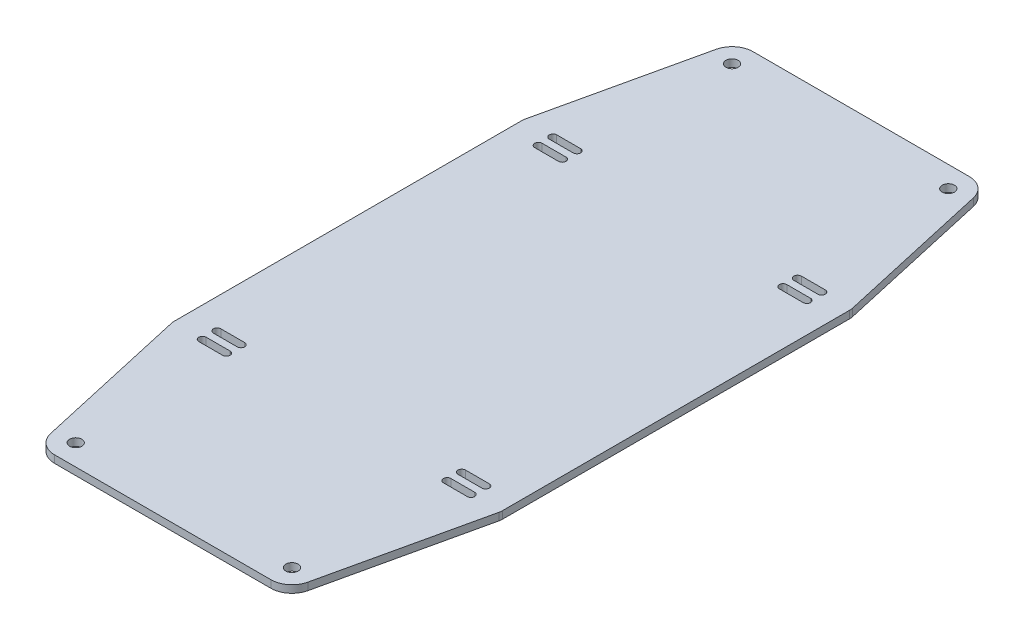
SolidWorks part; units mm, degrees
ref_plane "Front Plane" through (0, 0, 0) normal (0, 0, 1) x (1, 0, 0)
ref_plane "Top Plane" through (0, 0, 0) normal (0, 1, 0) x (1, 0, 0)
ref_plane "Right Plane" through (0, 0, 0) normal (1, 0, 0) x (0, 0, -1)
sketch "Sketch1" plane through (0, 0, 0) normal (0, 1, 0) x (1, 0, 0)
  line L1 (-139.979, 87.3459) -> (143.4878, 87.3459)
  line L2 (-139.979, 87.3459) -> (-139.979, -95.8674)
  line L3 (-139.979, -95.8674) -> (143.4878, -95.8674)
  line L4 (143.4878, 87.3459) -> (143.4878, -95.8674)
  dimension "D1" = 283.4668
  dimension "D2" = 183.2133
extrude "Boss-Extrude1" add sketch "Sketch1" along normal blind 3.175
sketch "Sketch2" plane through (0, 3.175, 0) normal (0, 1, 0) x (1, 0, 0)
  line L0 (14.6126, 63.1663) -> (128.9126, 63.1663)
  line L1 (14.6126, -79.8357) -> (128.9126, -79.8357)
  line L2 (14.6126, -79.8357) -> (14.6126, 66.2143)
  line L3 (14.6126, 66.2143) -> (128.9126, 66.2143)
  line L4 (128.9126, -79.8357) -> (128.9126, 66.2143)
  line L5 (14.6126, 61.5788) -> (24.7726, 61.5788) construction
  line L6 (14.6126, 63.1663) -> (24.7726, 63.1663)
  line L7 (14.6126, 59.9913) -> (24.7726, 59.9913)
  line L8 (14.6126, 67.8018) -> (24.7726, 67.8018) construction
  line L9 (14.6126, 69.3893) -> (24.7726, 69.3893)
  line L10 (14.6126, 66.2143) -> (24.7726, 66.2143)
  line L11 (118.7526, 61.5788) -> (128.9126, 61.5788) construction
  line L12 (118.7526, 63.1663) -> (128.9126, 63.1663)
  line L13 (118.7526, 59.9913) -> (128.9126, 59.9913)
  line L14 (118.7526, 67.8018) -> (128.9126, 67.8018) construction
  line L15 (118.7526, 69.3893) -> (128.9126, 69.3893)
  line L16 (118.7526, 66.2143) -> (128.9126, 66.2143)
  line L17 (14.6126, -6.8107) -> (128.9126, -6.8107)
  line L18 (118.7526, -75.2002) -> (128.9126, -75.2002) construction
  line L19 (118.7526, -76.7877) -> (128.9126, -76.7877)
  line L20 (118.7526, -73.6127) -> (128.9126, -73.6127)
  line L21 (118.7526, -81.4232) -> (128.9126, -81.4232) construction
  line L22 (118.7526, -83.0107) -> (128.9126, -83.0107)
  line L23 (118.7526, -79.8357) -> (128.9126, -79.8357)
  line L24 (14.6126, -75.2002) -> (24.7726, -75.2002) construction
  line L25 (14.6126, -76.7877) -> (24.7726, -76.7877)
  line L26 (14.6126, -73.6127) -> (24.7726, -73.6127)
  line L27 (14.6126, -81.4232) -> (24.7726, -81.4232) construction
  line L28 (14.6126, -83.0107) -> (24.7726, -83.0107)
  line L29 (14.6126, -79.8357) -> (24.7726, -79.8357)
  line L31 (1.9126, -79.8357) -> (1.9126, 78.9143)
  line L32 (1.9126, 78.9143) -> (141.6126, 78.9143)
  line L33 (141.6126, -79.8357) -> (141.6126, 78.9143)
  line L34 (14.6126, -67.1357) -> (128.9126, -67.1357)
  line L35 (14.6126, -92.5357) -> (128.9126, -92.5357)
  line L36 (128.9126, -92.5357) -> (141.6126, -92.5357)
  line L37 (141.6126, -92.5357) -> (141.6126, -79.8357)
  line L38 (14.6126, -92.5357) -> (1.9126, -92.5357)
  line L39 (1.9126, -92.5357) -> (1.9126, -79.8357)
  arc A0 (14.6126, 63.1663) -> (14.6126, 59.9913) centre (14.6126, 61.5788) ccw
  arc A1 (24.7726, 59.9913) -> (24.7726, 63.1663) centre (24.7726, 61.5788) ccw
  arc A2 (14.6126, 69.3893) -> (14.6126, 66.2143) centre (14.6126, 67.8018) ccw
  arc A3 (24.7726, 66.2143) -> (24.7726, 69.3893) centre (24.7726, 67.8018) ccw
  arc A4 (118.7526, 63.1663) -> (118.7526, 59.9913) centre (118.7526, 61.5788) ccw
  arc A5 (128.9126, 59.9913) -> (128.9126, 63.1663) centre (128.9126, 61.5788) ccw
  arc A6 (118.7526, 69.3893) -> (118.7526, 66.2143) centre (118.7526, 67.8018) ccw
  arc A7 (128.9126, 66.2143) -> (128.9126, 69.3893) centre (128.9126, 67.8018) ccw
  arc A8 (118.7526, -76.7877) -> (118.7526, -73.6127) centre (118.7526, -75.2002) cw
  arc A9 (128.9126, -73.6127) -> (128.9126, -76.7877) centre (128.9126, -75.2002) cw
  arc A10 (118.7526, -83.0107) -> (118.7526, -79.8357) centre (118.7526, -81.4232) cw
  arc A11 (128.9126, -79.8357) -> (128.9126, -83.0107) centre (128.9126, -81.4232) cw
  arc A12 (14.6126, -76.7877) -> (14.6126, -73.6127) centre (14.6126, -75.2002) cw
  arc A13 (24.7726, -73.6127) -> (24.7726, -76.7877) centre (24.7726, -75.2002) cw
  arc A14 (14.6126, -83.0107) -> (14.6126, -79.8357) centre (14.6126, -81.4232) cw
  arc A15 (24.7726, -79.8357) -> (24.7726, -83.0107) centre (24.7726, -81.4232) cw
  point P8 (19.6926, 61.5788)
  point P17 (19.6926, 67.8018)
  point P22 (123.8326, -75.2002)
  point P26 (123.8326, 61.5788)
  point P33 (123.8326, 67.8018)
  point P45 (123.8326, -81.4232)
  point P51 (19.6926, -75.2002)
  point P58 (19.6926, -81.4232)
  line M5 (-139.979, 87.3459) -> (-139.979, -95.8674)
  line M6 (-139.979, -95.8674) -> (143.4878, -95.8674)
  line M7 (143.4878, -95.8674) -> (143.4878, 87.3459)
  line M8 (143.4878, 87.3459) -> (-139.979, 87.3459)
  dimension "D1" = 12.7
  dimension "D2" = 114.3
  dimension "D3" = 12.7
extrude "Cut-Extrude1" cut sketch "Sketch2" against normal through all contours L38 L39 L31 L32 L33 L37 L36 L35 M8 M5 M6 M7 | L7 A1 L0 L2 | L2 A0 | L3 A3 L9 A2 | L0 A4 L13 L4 | L3 A7 L15 A6 | A11 L1 A10 L22 | A9 L4 | A8 L19 L4 L20 | L4 A5 | A15 L1 A14 L28 | A13 L26 L2 L25 | A12 L2
sketch "Sketch4" plane through (0, 3.175, 0) normal (0, 1, 0) x (1, 0, 0)
  line L1 (141.6126, 78.9143) -> (141.6126, 220.5913)
  line L2 (141.6126, -92.5357) -> (141.6126, -210.8334)
  line L3 (1.9126, 78.9143) -> (141.6126, 78.9143)
  line L4 (1.9126, 78.9143) -> (1.9126, 155.1143)
  line L5 (1.9126, 155.1143) -> (141.6126, 155.1143)
  line L6 (141.6126, 78.9143) -> (141.6126, 155.1143)
  line L8 (1.9126, -92.5357) -> (141.6126, -92.5357)
  line L9 (1.9126, -92.5357) -> (1.9126, -168.7357)
  line L10 (1.9126, -168.7357) -> (141.6126, -168.7357)
  line L11 (141.6126, -92.5357) -> (141.6126, -168.7357)
  line M19 (1.9126, -92.5357) -> (141.6126, -92.5357)
  line M21 (141.6126, 78.9143) -> (1.9126, 78.9143)
  dimension "D1" = 76.2
  dimension "D2" = 76.2
extrude "Boss-Extrude2" add sketch "Sketch4" against normal blind 3.175 contours L5 L4 L1 M21 | L9 L10 L2 M19
sketch "Sketch3" plane through (0, 3.175, 0) normal (0, 1, 0) x (1, 0, 0)
  line L0 (141.6126, -92.5357) -> (1.9126, -92.5357) construction
  line L5 (1.9126, 78.9143) -> (141.6126, 78.9143)
  line L6 (1.9126, 78.9143) -> (1.9126, -92.5357)
  line L7 (1.9126, -92.5357) -> (141.6126, -92.5357)
  line L8 (141.6126, 78.9143) -> (141.6126, -92.5357)
  line L9 (1.9126, 78.9143) -> (141.6126, -92.5357) construction
  line L10 (1.9126, -92.5357) -> (141.6126, 78.9143) construction
  line L11 (1.9126, 78.9143) -> (141.6126, 78.9143) construction
  line L12 (141.6126, -168.7357) -> (141.6126, 155.1143) construction
  line L13 (1.9126, -168.7357) -> (1.9126, 155.1143) construction
  line L15 (117.8001, 132.8893) -> (25.7251, 132.8893)
  line L16 (117.8001, 132.8893) -> (117.8001, -146.5107)
  line L17 (117.8001, -146.5107) -> (25.7251, -146.5107)
  line L18 (25.7251, 132.8893) -> (25.7251, -146.5107)
  line L19 (117.8001, 132.8893) -> (25.7251, -146.5107) construction
  line L20 (117.8001, -146.5107) -> (25.7251, 132.8893) construction
  circle A0 centre (117.8001, 132.8893) radius 2.6
  circle A1 centre (117.8001, -146.5107) radius 2.6
  circle A2 centre (25.7251, -146.5107) radius 2.6
  circle A3 centre (25.7251, 132.8893) radius 2.6
  point P0 (71.7626, -6.8107)
  point P4 (71.7626, -6.8107)
  dimension "D3" = 5.2
  dimension "D4" = 5.2
  dimension "D5" = 5.2
  dimension "D6" = 5.2
  dimension "D1" = 279.4
  dimension "D2" = 92.075
extrude "Cut-Extrude2" cut sketch "Sketch3" against normal through all contours L15 A3 L18 | L18 A3 L15 | L16 A0 L15 | L15 A0 L16 | L17 A1 L16 | L16 A1 L17 | L18 A2 L17 | L17 A2 L18
sketch "Sketch5" plane through (0, 3.175, 0) normal (0, 1, 0) x (1, 0, 0)
  line L8 (16.9933, 134.8532) -> (1.9126, 67.8018)
  line L9 (126.532, 134.8532) -> (141.6126, 67.8018)
  line L10 (141.6126, -81.4232) -> (126.532, -148.4746)
  line L11 (16.9933, -148.4746) -> (1.9126, -81.4232)
  line L12 (117.8001, 141.8393) -> (25.7251, 141.8393)
  line L13 (117.8001, -155.4607) -> (25.7251, -155.4607)
  line L14 (141.6126, -168.7357) -> (141.6126, 155.1143) construction
  line L15 (141.6126, 67.8018) -> (141.6126, -81.4232)
  line L16 (1.9126, -168.7357) -> (1.9126, 155.1143) construction
  line L17 (1.9126, 67.8018) -> (1.9126, -81.4232)
  circle A2 centre (117.8001, 132.8893) radius 8.95
  circle A3 centre (117.8001, 132.8893) radius 8.95
  circle A5 centre (25.7251, 132.8893) radius 8.95
  circle A6 centre (25.7251, 132.8893) radius 8.95
  circle A8 centre (25.7251, -146.5107) radius 8.95
  circle A9 centre (25.7251, -146.5107) radius 8.95
  circle A11 centre (117.8001, -146.5107) radius 8.95
  circle A12 centre (117.8001, -146.5107) radius 8.95
  arc A14 (128.9126, -89.3607) -> (128.9126, -73.4857) centre (128.9126, -81.4232) ccw
  arc A15 (128.9126, -89.3607) -> (128.9126, -73.4857) centre (128.9126, -81.4232) ccw
  arc A17 (128.9126, 59.8643) -> (128.9126, 75.7393) centre (128.9126, 67.8018) ccw
  arc A18 (128.9126, 59.8643) -> (128.9126, 75.7393) centre (128.9126, 67.8018) ccw
  arc A20 (14.6126, -73.4857) -> (14.6126, -89.3607) centre (14.6126, -81.4232) ccw
  arc A21 (14.6126, -73.4857) -> (14.6126, -89.3607) centre (14.6126, -81.4232) ccw
  arc A23 (14.6126, 75.7393) -> (14.6126, 59.8643) centre (14.6126, 67.8018) ccw
  arc A24 (14.6126, 75.7393) -> (14.6126, 59.8643) centre (14.6126, 67.8018) ccw
  line M29 (1.9126, 155.1143) -> (1.9126, -168.7357)
  line M30 (1.9126, -168.7357) -> (141.6126, -168.7357)
  line M31 (141.6126, -168.7357) -> (141.6126, 155.1143)
  line M32 (141.6126, 155.1143) -> (1.9126, 155.1143)
  dimension "D1" = 6.35
  dimension "D2" = 6.35
  dimension "D3" = 6.35
  dimension "D4" = 6.35
  dimension "D5" = 6.35
  dimension "D6" = 6.35
  dimension "D7" = 6.35
  dimension "D8" = 6.35
extrude "Cut-Extrude3" cut sketch "Sketch5" against normal through all both and the other way through all contours A6 L12 A3 L9 L8 M31 M32 M29 | A12 L13 A9 L11 L10 M29 M30 M31
sketch "Sketch6" plane through (0, 3.175, 0) normal (0, 1, 0) x (1, 0, 0)
  line L6 (118.7526, 59.8643) -> (128.9126, 59.8643)
  line L7 (128.9126, 75.7393) -> (118.7526, 75.7393)
  line L8 (118.7526, 59.8643) -> (128.9126, 59.8643)
  line L9 (128.9126, 75.7393) -> (118.7526, 75.7393)
  line L13 (118.7526, 75.7393) -> (24.7726, 75.7393)
  line L14 (128.9126, 75.7393) -> (130.0645, 75.7393)
  line L15 (14.6126, 59.8643) -> (24.7726, 59.8643)
  line L16 (24.7726, 75.7393) -> (14.6126, 75.7393)
  line L17 (14.6126, 59.8643) -> (24.7726, 59.8643)
  line L18 (24.7726, 75.7393) -> (14.6126, 75.7393)
  line L19 (14.6126, 75.7393) -> (13.4608, 75.7393)
  line L20 (141.6126, -6.8107) -> (1.9126, -6.8107)
  line L21 (141.6126, -81.4232) -> (141.6126, 67.8018) construction
  line L22 (1.9126, -81.4232) -> (1.9126, 67.8018) construction
  line L23 (117.3401, -145.9357) -> (26.1852, -145.9357)
  line L24 (26.1852, 132.3143) -> (11.4376, 66.7438)
  line L25 (11.4376, 66.7438) -> (11.4376, -80.3653)
  line L26 (11.4376, -80.3653) -> (26.1852, -145.9357)
  line L27 (26.1852, -145.9357) -> (117.3401, -145.9357)
  line L28 (117.3401, -145.9357) -> (132.0876, -80.3653)
  line L29 (132.0876, -80.3653) -> (132.0876, 66.7438)
  line L30 (132.0876, 66.7438) -> (117.3401, 132.3143)
  line L31 (117.3401, 132.3143) -> (26.1852, 132.3143)
  line L32 (26.1852, 132.3143) -> (11.4376, 66.7438)
  line L33 (11.4376, 66.7438) -> (11.4376, -80.3653)
  line L34 (11.4376, -80.3653) -> (26.1852, -145.9357)
  line L35 (26.1852, -145.9357) -> (117.3401, -145.9357)
  line L36 (117.3401, -145.9357) -> (132.0876, -80.3653)
  line L37 (132.0876, -80.3653) -> (132.0876, 66.7438)
  line L38 (132.0876, 66.7438) -> (117.3401, 132.3143)
  line L39 (117.3401, 132.3143) -> (26.1852, 132.3143)
  line L40 (132.0876, -80.3653) -> (117.3401, -145.9357)
  line L41 (26.1852, -145.9357) -> (11.4376, -80.3653)
  line L42 (14.6126, -89.3607) -> (13.4608, -89.3607)
  line L43 (24.7726, -89.3607) -> (14.6126, -89.3607)
  line L44 (14.6126, -73.4857) -> (24.7726, -73.4857)
  line L45 (128.9126, -89.3607) -> (130.0645, -89.3607)
  line L46 (118.7526, -89.3607) -> (24.7726, -89.3607)
  line L47 (128.9126, -89.3607) -> (118.7526, -89.3607)
  line L48 (118.7526, -73.4857) -> (128.9126, -73.4857)
  circle A2 centre (117.8001, 132.8893) radius 8.95
  circle A3 centre (117.8001, 132.8893) radius 8.95
  circle A5 centre (25.7251, 132.8893) radius 8.95
  circle A6 centre (25.7251, 132.8893) radius 8.95
  arc A12 (128.9126, 59.8643) -> (128.9126, 75.7393) centre (128.9126, 67.8018) ccw
  arc A13 (118.7526, 75.7393) -> (118.7526, 59.8643) centre (118.7526, 67.8018) ccw
  arc A14 (128.9126, 59.8643) -> (128.9126, 75.7393) centre (128.9126, 67.8018) ccw
  arc A15 (118.7526, 75.7393) -> (118.7526, 59.8643) centre (118.7526, 67.8018) ccw
  arc A20 (24.7726, -73.4857) -> (24.7726, -89.3607) centre (24.7726, -81.4232) cw
  arc A22 (14.6126, -89.3607) -> (14.6126, -73.4857) centre (14.6126, -81.4232) cw
  arc A24 (14.6126, 75.7393) -> (14.6126, 59.8643) centre (14.6126, 67.8018) ccw
  arc A26 (24.7726, 59.8643) -> (24.7726, 75.7393) centre (24.7726, 67.8018) ccw
  arc A27 (14.6126, 75.7393) -> (14.6126, 59.8643) centre (14.6126, 67.8018) ccw
  arc A28 (24.7726, 59.8643) -> (24.7726, 75.7393) centre (24.7726, 67.8018) ccw
  arc A29 (118.7526, -89.3607) -> (118.7526, -73.4857) centre (118.7526, -81.4232) cw
  arc A30 (128.9126, -73.4857) -> (128.9126, -89.3607) centre (128.9126, -81.4232) cw
  circle A31 centre (25.7251, -146.5107) radius 8.95
  circle A32 centre (117.8001, -146.5107) radius 8.95
  dimension "D1" = 6.35
  dimension "D2" = 6.35
  dimension "D3" = 9.525
  dimension "D4" = 6.35
  dimension "D5" = 6.35
fillet "Fillet1" radius 6.35 4 edges at (1.9126, 1.5875, 81.4232) (141.6126, 1.5875, 81.4232) (141.6126, 1.5875, -67.8018) (1.9126, 1.5875, -67.8018)
